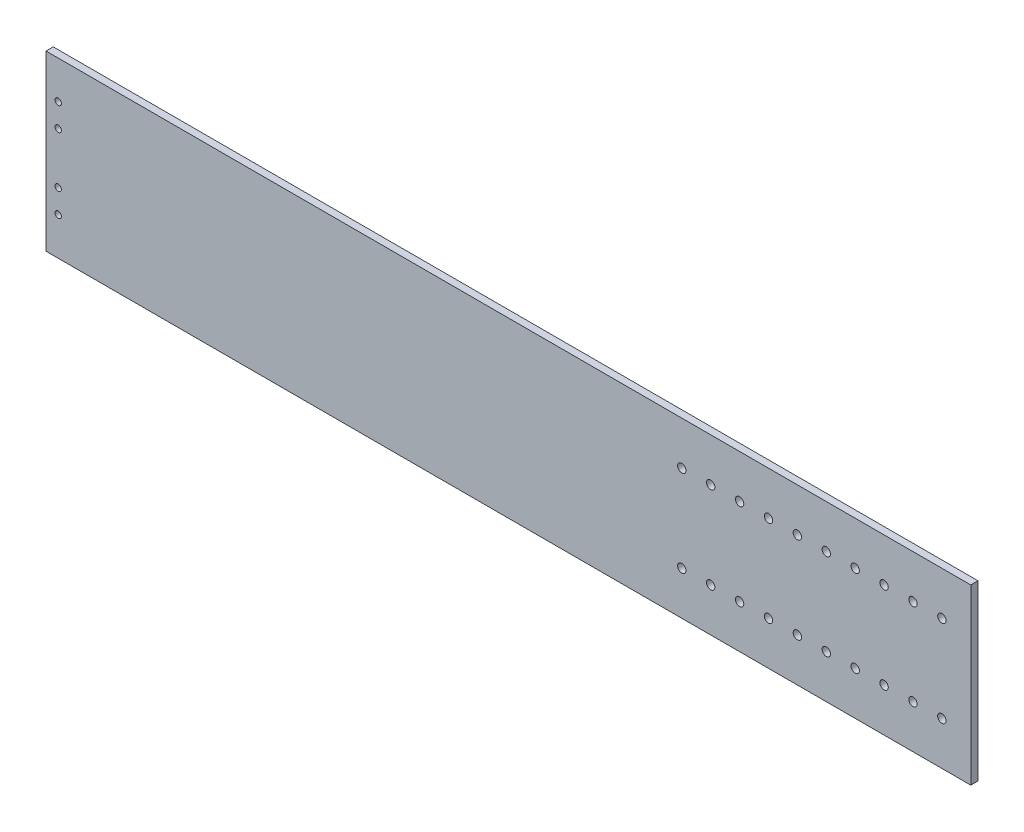
SolidWorks part; units mm, degrees
ref_plane "Front" through (0, 0, 0) normal (0, 0, 1) x (1, 0, 0)
ref_plane "Top" through (0, 0, 0) normal (0, 1, 0) x (1, 0, 0)
ref_plane "Right" through (0, 0, 0) normal (1, 0, 0) x (0, 0, -1)
sketch "Sketch1" plane through (0, 0, 0) normal (0, 0, 1) x (1, 0, 0)
  line L1 (0, 0) -> (406.4, 0)
  line L2 (0, 0) -> (0, 76.2)
  line L3 (0, 76.2) -> (406.4, 76.2)
  line L4 (406.4, 0) -> (406.4, 76.2)
  dimension "D1" = 406.4
  dimension "D2" = 76.2
extrude "basic_plank" add sketch "Sketch1" along normal blind 3.175
sketch "Sketch5" plane through (0, 0, 3.175) normal (0, 0, 1) x (1, 0, 0)
  line L0 (406.4, 76.2) -> (0, 76.2) construction
  line L3 (0, 76.2) -> (0, 0) construction
  line L4 (0, 38.1) -> (42.978, 38.1) construction
  line L5 (5.3594, 59.5884) -> (5.3594, 16.6116) construction
  circle A0 centre (5.3594, 59.5884) radius 1.397
  circle A1 centre (5.3594, 16.6116) radius 1.397
  circle A2 centre (5.3594, 49.3014) radius 1.397
  circle A3 centre (5.3594, 26.8986) radius 1.397
  dimension "D1" = 2.794
  dimension "D4" = 2.794
  dimension "D2" = 16.6116
  dimension "D3" = 5.3594
  dimension "D5" = 10.287
extrude "bracket holes" cut sketch "Sketch5" against normal through all
sketch "Sketch6" plane through (0, 0, 3.175) normal (0, 0, 1) x (1, 0, 0)
  line L0 (406.4, 0) -> (406.4, 76.2) construction
  line L1 (406.4, 76.2) -> (0, 76.2) construction
  line L2 (406.4, 38.1) -> (357.2264, 38.1) construction
  circle A0 centre (279.4, 57.15) radius 1.8415
  circle A1 centre (292.1, 57.15) radius 1.8415
  circle A2 centre (304.8, 57.15) radius 1.8415
  circle A3 centre (317.5, 57.15) radius 1.8415
  circle A4 centre (330.2, 57.15) radius 1.8415
  circle A5 centre (342.9, 57.15) radius 1.8415
  circle A6 centre (355.6, 57.15) radius 1.8415
  circle A7 centre (368.3, 57.15) radius 1.8415
  circle A8 centre (381, 57.15) radius 1.8415
  circle A9 centre (393.7, 57.15) radius 1.8415
  circle A10 centre (393.7, 19.05) radius 1.8415
  circle A11 centre (381, 19.05) radius 1.8415
  circle A12 centre (368.3, 19.05) radius 1.8415
  circle A13 centre (355.6, 19.05) radius 1.8415
  circle A14 centre (342.9, 19.05) radius 1.8415
  circle A15 centre (330.2, 19.05) radius 1.8415
  circle A16 centre (317.5, 19.05) radius 1.8415
  circle A17 centre (304.8, 19.05) radius 1.8415
  circle A18 centre (292.1, 19.05) radius 1.8415
  circle A19 centre (279.4, 19.05) radius 1.8415
  dimension "D1" = 3.683
  dimension "D3" = 19.05
  dimension "D2" = 127
  dimension "D4" = 10
extrude "placement holes" cut sketch "Sketch6" against normal through all
